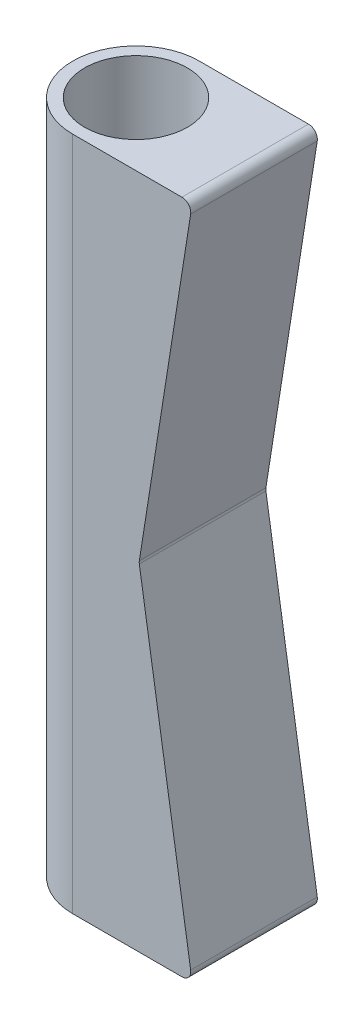
SolidWorks part; units mm, degrees
ref_plane "Front Plane" through (0, 0, 0) normal (0, 0, 1) x (1, 0, 0)
ref_plane "Top Plane" through (0, 0, 0) normal (0, 1, 0) x (1, 0, 0)
ref_plane "Right Plane" through (0, 0, 0) normal (1, 0, 0) x (0, 0, -1)
sketch "Sketch1" plane through (0, 0, 0) normal (0, 1, 0) x (1, 0, 0)
  circle A0 centre (0, 0) radius 11.6125
  circle A1 centre (0, 0) radius 14.2875
  dimension "D1" = 23.225
  dimension "D2" = 28.575
extrude "Boss-Extrude1" add sketch "Sketch1" along normal blind 152.4
ref_plane "Plane1" through (14.2875, 0, 0) normal (1, 0, 0) x (0, 0, -1)
sketch "Sketch2" plane through (14.2875, 0, 0) normal (1, 0, 0) x (0, 0, -1)
  line L1 (14.2875, 0) -> (-14.2875, 0)
  line L2 (14.2875, 0) -> (14.2875, 152.4)
  line L3 (14.2875, 152.4) -> (-14.2875, 152.4)
  line L4 (-14.2875, 0) -> (-14.2875, 152.4)
extrude "Boss-Extrude2" add sketch "Sketch2" along normal blind 12.7 separate body
sketch "Sketch3" plane through (0, 152.4, 0) normal (0, 1, 0) x (1, 0, 0)
  line L0 (14.2875, -14.2875) -> (0, -14.2875)
  line L1 (14.2875, 14.2875) -> (0, 14.2875)
  line L4 (14.2875, 14.2875) -> (14.2875, -14.2875)
  line L5 (14.2875, -14.2875) -> (26.9875, -14.2875)
  line L6 (26.9875, -14.2875) -> (26.9875, 14.2875)
  line L7 (26.9875, 14.2875) -> (14.2875, 14.2875)
  line L9 (14.2875, -14.2875) -> (26.9875, -14.2875)
  line L10 (26.9875, -14.2875) -> (26.9875, 14.2875)
  line L11 (26.9875, 14.2875) -> (14.2875, 14.2875)
  arc A0 (0, -14.2875) -> (0, 14.2875) centre (0, 0) ccw
  dimension "D1" = 0
extrude "Boss-Extrude3" add sketch "Sketch3" against normal through all
sketch "Sketch5" plane through (0, 0, 14.2875) normal (0, 0, 1) x (1, 0, 0)
  line L0 (26.9875, 0) -> (14.9875, 76.2)
  line L1 (14.9875, 76.2) -> (26.9875, 152.4)
  line L2 (0, 0) -> (26.9875, 0) construction
  line L4 (26.9875, 0) -> (26.9875, 152.4) construction
  line L5 (26.9875, 0) -> (26.9875, 152.4)
  dimension "D1" = 76.2
  dimension "D2" = 12
extrude "Cut-Extrude1" cut sketch "Sketch5" against normal through all
fillet "Fillet1" radius 2 3 edges at (26.9875, 152.4, 0) (14.9875, 76.2, 0) (26.9875, 0, 0)
